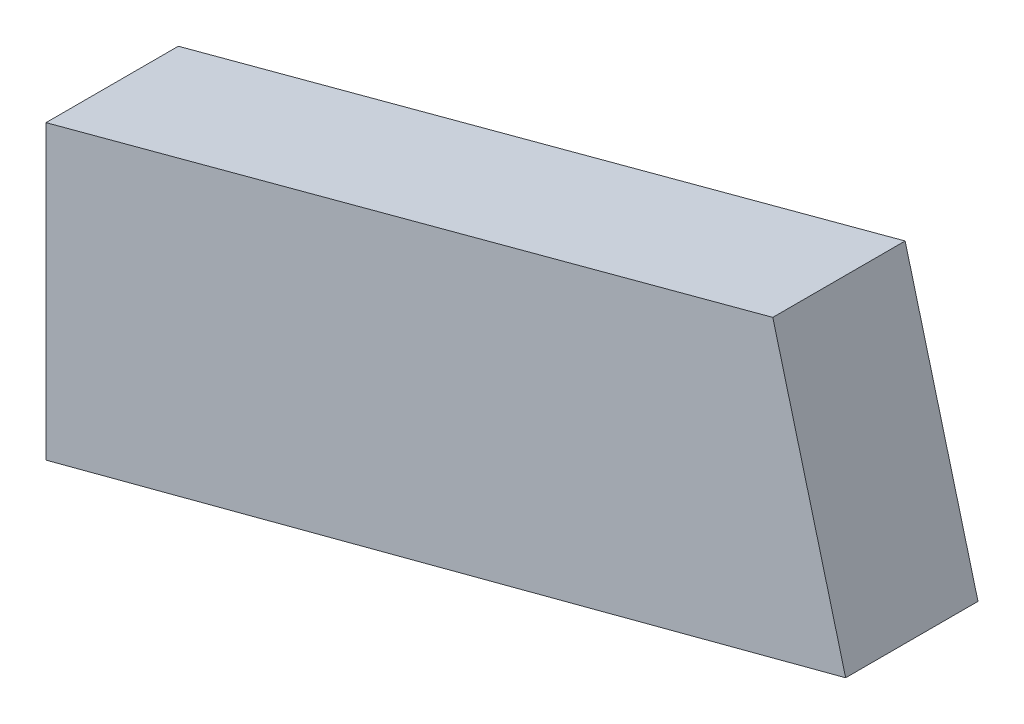
SolidWorks part; units mm, degrees
ref_plane "Front Plane" through (0, 0, 0) normal (0, 0, 1) x (1, 0, 0)
ref_plane "Top Plane" through (0, 0, 0) normal (0, 1, 0) x (1, 0, 0)
ref_plane "Right Plane" through (0, 0, 0) normal (1, 0, 0) x (0, 0, -1)
sketch "Sketch1" plane through (0, 0, 0) normal (0, 0, 1) x (1, 0, 0)
  line L0 (0, 0) -> (72.5107, 19.1623)
  line L1 (72.5107, 19.1623) -> (65.904, 44.1623)
  line L2 (65.904, 44.1623) -> (0, 26.5033)
  line L3 (0, 26.5033) -> (0, 0)
  line L4 (0, 26.5033) -> (0, 46.7021) construction
  dimension "D1" = 75
  dimension "D2" = 75
  dimension "D3" = 25
extrude "Boss-Extrude1" add sketch "Sketch1" along normal blind 12
